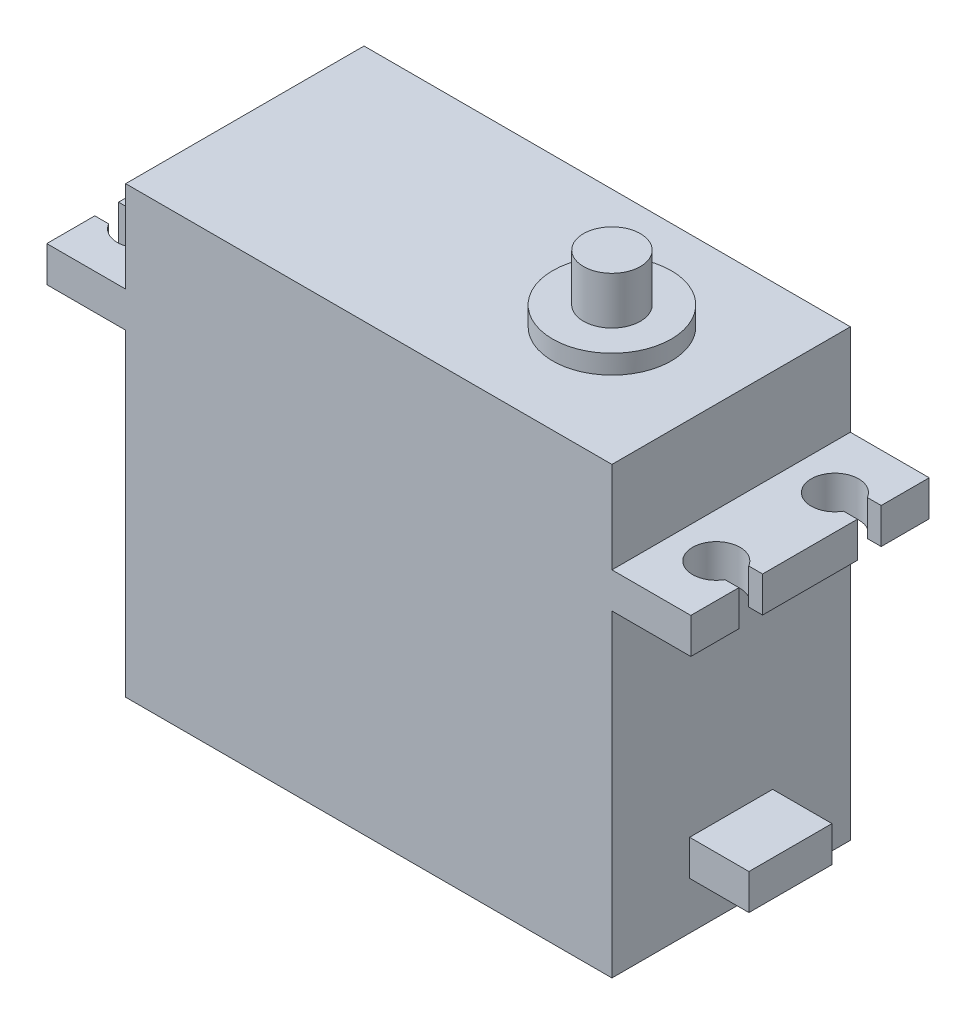
SolidWorks part; units mm, degrees
ref_plane "Front Plane" through (0, 0, 0) normal (0, 0, 1) x (1, 0, 0)
ref_plane "Top Plane" through (0, 0, 0) normal (0, 1, 0) x (1, 0, 0)
ref_plane "Right Plane" through (0, 0, 0) normal (1, 0, 0) x (0, 0, -1)
sketch "Sketch2" plane through (0, 0, 0) normal (0, 1, 0) x (1, 0, 0)
  line L0 (0, 0) -> (0, 10.05) construction
  line L1 (0, 0) -> (10.05, 0) construction
  line L2 (0, 0) -> (0, -10.05) construction
  line L3 (0, 0) -> (-30.95, 0) construction
  line L4 (-34.7, 5) -> (-34.7, -5) construction
  line L5 (-30.95, 10.05) -> (10.05, 10.05)
  line L6 (-30.95, 10.05) -> (-30.95, -10.05)
  line L7 (-30.95, -10.05) -> (10.05, -10.05)
  line L8 (10.05, 10.05) -> (10.05, -10.05)
  line L9 (-30.95, 10.05) -> (-37.6, 10.05) construction
  line L10 (-37.6, 10.05) -> (-37.6, -10.05) construction
  line L11 (-37.6, -10.05) -> (-30.95, -10.05) construction
  line L12 (-10.45, 10.05) -> (-10.45, -10.05) construction
  line L13 (13.8, 5) -> (13.8, -5) construction
  line L14 (-36.7, 5) -> (-37.6, 5) construction
  line L15 (10.05, 10.05) -> (16.7, 10.05) construction
  line L16 (16.7, 10.05) -> (16.7, -10.05) construction
  line L17 (16.7, -10.05) -> (10.05, -10.05) construction
  line L18 (10.05, 3.5) -> (15.05, 3.5) construction
  line L19 (15.05, 3.5) -> (15.05, -3.5) construction
  line L20 (15.05, -3.5) -> (10.05, -3.5) construction
  circle A0 centre (0, 0) radius 2.4
  circle A1 centre (0, 0) radius 10.05 construction
  circle A2 centre (-34.7, 5) radius 2
  circle A3 centre (-34.7, -5) radius 2
  circle A4 centre (13.8, -5) radius 2
  circle A5 centre (13.8, 5) radius 2
  circle A6 centre (0, 0) radius 5 construction
  dimension "D1" = 4.8
  dimension "D6" = 4
  dimension "D8" = 10
  dimension "D2" = 41
  dimension "D3" = 20.1
  dimension "D4" = 10
  dimension "D5" = 48.5
  dimension "D7" = 0.9
  dimension "D9" = 54.3
  dimension "D10" = 7
  dimension "D11" = 5
sketch "Sketch3" plane through (0, 0, 0) normal (0, 0, 1) x (1, 0, 0)
  line L0 (-30.95, 0) -> (-30.95, 26.8)
  line L1 (-30.95, 26.8) -> (-37.6, 26.8)
  line L2 (-37.6, 26.8) -> (-37.6, 29.8)
  line L3 (-37.6, 29.8) -> (-30.95, 29.8)
  line L4 (-30.95, 29.8) -> (-30.95, 37.5)
  line L5 (-30.95, 37.5) -> (10.05, 37.5)
  line L6 (10.05, 37.5) -> (10.05, 29.8)
  line L7 (10.05, 29.8) -> (16.7, 29.8)
  line L8 (16.7, 29.8) -> (16.7, 26.8)
  line L9 (16.7, 26.8) -> (10.05, 26.8)
  line L10 (10.05, 26.8) -> (10.05, 0)
  line L11 (10.05, 0) -> (-30.95, 0)
  line L12 (-10.45, 0) -> (-10.45, 37.5) construction
  line L13 (2.4, 0) -> (2.4, 43.1) construction
  line L14 (2.4, 0) -> (-2.4, 0) construction
  line L15 (2.4, 43.1) -> (-2.4, 43.1) construction
  line L16 (-2.4, 43.1) -> (-2.4, 0) construction
  line L17 (10.05, 0) -> (-10.05, 0) construction
  line L18 (-5, 39.1) -> (5, 39.1) construction
  line L19 (-5, 0) -> (-5, 39.1) construction
  line L20 (5, 39.1) -> (5, 0) construction
  line L21 (10.05, 4) -> (15.05, 4) construction
  line L22 (15.05, 4) -> (15.05, 7) construction
  line L23 (15.05, 7) -> (10.05, 7) construction
  line L24 (5, 39.1) -> (19.7, 39.1) construction
  line L26 (19.7, 39.1) -> (19.7, 26.8) construction
  line L28 (16.7, 26.8) -> (19.7, 26.8) construction
  dimension "D1" = 26.8
  dimension "D2" = 3
  dimension "D3" = 4
  dimension "D4" = 39.1
  dimension "D5" = 1.6
  dimension "D6" = 12.3
  dimension "D7" = 7
  dimension "D8" = 4
  dimension "D9" = 37.5
extrude "Boss-Extrude1" add sketch "Sketch3" along normal up to vertex (10.05 mm away) from vertex at -10.05 starting at point (-30.95, 0, -10.05)
sketch "Sketch4" plane through (0, 29.8, 0) normal (0, 1, 0) x (1, 0, 0)
  line L0 (-10.45, 10.05) -> (-10.45, -10.05) construction
  line L1 (-10.45, 10.05) -> (-10.45, -10.05) construction
  line L2 (-37.6, 10.05) -> (-37.6, -10.05) construction
  line L4 (-37.6, 6) -> (-37.6, 4)
  line L5 (16.7, -6) -> (15.5321, -6)
  line L6 (-10.45, 0) -> (-37.6, 0) construction
  line L7 (-37.6, 4) -> (-36.4321, 4)
  line L8 (-37.6, 6) -> (-36.4321, 6)
  line L9 (-34.7, 5) -> (-37.6, 5) construction
  line L10 (-37.6, -4) -> (-37.6, -6)
  line L11 (-37.6, -4) -> (-36.4321, -4)
  line L12 (-37.6, -6) -> (-36.4321, -6)
  line L13 (16.7, -4) -> (16.7, -6)
  line L14 (16.7, -4) -> (15.5321, -4)
  line L15 (16.7, 4) -> (15.5321, 4)
  line L16 (16.7, 6) -> (16.7, 4)
  line L17 (16.7, 6) -> (15.5321, 6)
  circle A0 centre (-34.7, -5) radius 2 construction
  circle A1 centre (-34.7, 5) radius 2 construction
  circle A2 centre (13.8, 5) radius 2 construction
  circle A3 centre (13.8, -5) radius 2 construction
  arc A4 (-36.4321, -6) -> (-36.4321, -4) centre (-34.7, -5) ccw
  arc A5 (-36.4321, 4) -> (-36.4321, 6) centre (-34.7, 5) ccw
  arc A6 (15.5321, 6) -> (15.5321, 4) centre (13.8, 5) ccw
  arc A7 (15.5321, -4) -> (15.5321, -6) centre (13.8, -5) ccw
  dimension "D1" = 2
extrude "Cut-Extrude1" cut sketch "Sketch4" against normal through all
sketch "Sketch5" plane through (0, 37.5, 0) normal (0, 1, 0) x (1, 0, 0)
  circle A0 centre (0, 0) radius 5 construction
  circle A1 centre (0, 0) radius 5
extrude "Boss-Extrude2" add sketch "Sketch5" along normal up to vertex (1.6 mm away) up to point (-5, 39.1, 0)
sketch "Sketch6" plane through (0, 39.1, 0) normal (0, 1, 0) x (1, 0, 0)
  circle A0 centre (0, 0) radius 2.4 construction
  circle A1 centre (0, 0) radius 2.4
extrude "Boss-Extrude3" add sketch "Sketch6" along normal up to vertex (4 mm away) up to point (-2.4, 43.1, 0)
sketch "Sketch7" plane through (0, 39.1, 0) normal (0, 1, 0) x (1, 0, 0)
  circle A0 centre (0, 0) radius 2.85
  dimension "D1" = 5.7
sketch "Sketch8" plane through (10.05, 0, 0) normal (1, 0, 0) x (0, 0, -1)
  line L1 (-3.5, 7) -> (3.5, 7)
  line L2 (-3.5, 7) -> (-3.5, 4)
  line L3 (-3.5, 4) -> (3.5, 4)
  line L4 (3.5, 7) -> (3.5, 4)
extrude "Boss-Extrude4" add sketch "Sketch8" along normal up to vertex (5 mm away) up to point (15.05, 7, 0)
